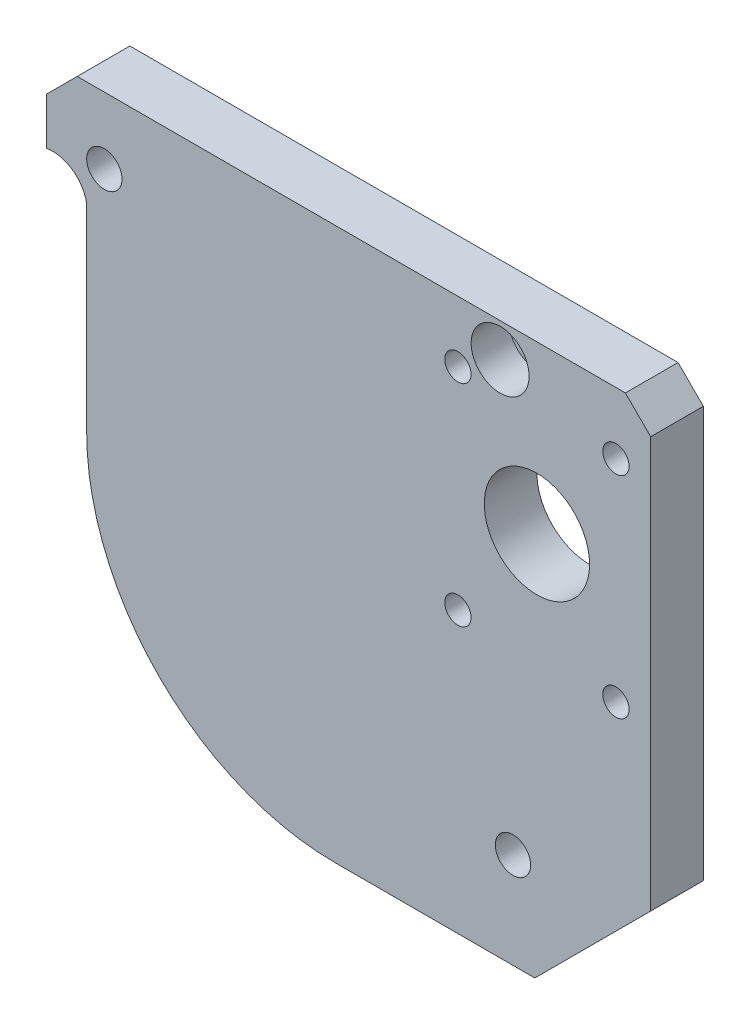
SolidWorks part; units mm, degrees
ref_plane "Front Plane" through (0, 0, 0) normal (0, 0, 1) x (1, 0, 0)
ref_plane "Top Plane" through (0, 0, 0) normal (0, 1, 0) x (1, 0, 0)
ref_plane "Right Plane" through (0, 0, 0) normal (1, 0, 0) x (0, 0, -1)
sketch "Sketch1" plane through (0, 0, 0) normal (0, 0, 1) x (1, 0, 0)
  line L0 (0, 0) -> (0, 66.548)
  line L1 (0, 66.548) -> (72.8218, 66.548)
  line L2 (72.8218, 66.548) -> (72.8218, 0)
  line L3 (72.8218, 0) -> (0, 0)
  dimension "D1" = 66.548
  dimension "D2" = 72.8218
extrude "Boss-Extrude1" add sketch "Sketch1" along normal blind 6.35
sketch "Sketch2" plane through (0, 0, 6.35) normal (0, 0, 1) x (1, 0, 0)
  line L0 (72.8218, 0) -> (72.8218, 66.548) construction
  line L1 (72.8218, 66.548) -> (0, 66.548) construction
  circle A0 centre (59.1058, 46.482) radius 6.35
  dimension "D1" = 12.7
  dimension "D2" = 13.716
  dimension "D3" = 20.066
extrude "Cut-Extrude1" cut sketch "Sketch2" against normal through all
sketch "Sketch3" plane through (0, 0, 6.35) normal (0, 0, 1) x (1, 0, 0)
  line L0 (0, 0) -> (72.8218, 0) construction
  line L1 (72.8218, 0) -> (72.8218, 66.548) construction
  circle A0 centre (56.2166, 11.5252) radius 2.1272
  dimension "D1" = 4.2545
  dimension "D2" = 11.5252
  dimension "D3" = 16.6052
extrude "Cut-Extrude2" cut sketch "Sketch3" against normal through all
sketch "Sketch4" plane through (0, 0, 6.35) normal (0, 0, 1) x (1, 0, 0)
  line L0 (0, 66.548) -> (0, 0) construction
  line L1 (72.8218, 66.548) -> (0, 66.548) construction
  circle A0 centre (6.9532, 58.5152) radius 2.1273
  dimension "D1" = 4.2545
  dimension "D2" = 6.9532
  dimension "D3" = 8.0328
extrude "Cut-Extrude3" cut sketch "Sketch4" against normal through all
sketch "Sketch5" plane through (0, 0, 6.35) normal (0, 0, 1) x (1, 0, 0)
  line L0 (72.8218, 66.548) -> (0, 66.548) construction
  line L1 (72.8218, 0) -> (72.8218, 66.548) construction
  circle A0 centre (54.6672, 62.465) radius 2.1272
  dimension "D1" = 4.2545
  dimension "D2" = 4.0831
  dimension "D3" = 18.1546
extrude "Cut-Extrude4" cut sketch "Sketch5" against normal through all
sketch "Sketch6" plane through (0, 0, 6.35) normal (0, 0, 1) x (1, 0, 0)
  circle A0 centre (54.6672, 62.465) radius 3.4925
  dimension "D1" = 6.985
extrude "Cut-Extrude5" cut sketch "Sketch6" against normal blind 4.572
hole_wizard "1/8 (0.125) Diameter Hole1" positions "Sketch8" profile "Sketch7" hole size "1/8" standard "Ansi Inch"
sketch "Sketch8" plane through (0, 0, 6.35) normal (0, 0, 1) x (1, 0, 0)
  circle A0 centre (59.1058, 46.482) radius 6.35 construction
  point P0 (49.5808, 59.182)
  point P1 (68.6308, 59.1091)
  point P3 (68.6307, 33.7091)
  point P5 (49.5808, 33.782)
  dimension "D1" = 12.7
  dimension "D2" = 9.525
  dimension "D3" = 19.05
  dimension "D4" = 25.4
  dimension "D5" = 19.05
  dimension "D6" = 25.4
  dimension "D7" = 9.525
sketch "Sketch7" plane through (49.5808, 59.182, 6.35) normal (1, 0, 0) x (0, -1, 0)
  line L0 (0, 0) -> (0, 26.3539)
  line L1 (0, 26.3539) -> (1.5875, 25.4)
  line L2 (1.5875, 25.4) -> (1.5875, 0)
  line L5 (1.5875, 0) -> (0, 0)
  line L10 (0, 26.3539) -> (-1.5875, 25.4) construction
  line L11 (0, -6.35) -> (0, 107.95) construction
  dimension "Hole Dia." = 3.175
  dimension "Hole Depth" = 25.4
  dimension "Drill Angle" = 118
sketch "Sketch9" plane through (0, 0, 6.35) normal (0, 0, 1) x (1, 0, 0)
  line L0 (72.8218, 13.97) -> (58.8518, 0)
  line L1 (72.8218, 0) -> (72.8218, 66.548) construction
  line L2 (0, 0) -> (72.8218, 0) construction
  line L3 (58.8518, 0) -> (72.8218, 0)
  line L4 (72.8218, 0) -> (72.8218, 13.97)
  dimension "D1" = 13.97
extrude "Cut-Extrude6" cut sketch "Sketch9" against normal through all
sketch "Sketch10" plane through (0, 0, 6.35) normal (0, 0, 1) x (1, 0, 0)
  line L0 (3.683, 66.548) -> (0, 62.865)
  line L1 (72.8218, 66.548) -> (0, 66.548) construction
  line L2 (0, 66.548) -> (0, 0) construction
  line L3 (0, 62.865) -> (0, 66.548)
  line L4 (0, 66.548) -> (3.683, 66.548)
  dimension "D1" = 3.683
extrude "Cut-Extrude7" cut sketch "Sketch10" against normal through all
sketch "Sketch11" plane through (0, 0, 6.35) normal (0, 0, 1) x (1, 0, 0)
  line L0 (4.826, 0) -> (4.826, 24.6833) construction
  line L2 (0, 62.865) -> (0, 0) construction
  line L3 (-5.4083, 57.1925) -> (14.8838, 57.1925) construction
  line L4 (4.826, 53.831) -> (4.826, 0)
  line L5 (0, 0) -> (58.8518, 0) construction
  line L6 (4.826, 0) -> (0, 0)
  line L7 (0, 0) -> (0, 57.1925)
  arc A0 (0, 57.1925) -> (4.826, 53.831) centre (0.7323, 53.0988) cw
  dimension "D1" = 4.826
extrude "Cut-Extrude8" cut sketch "Sketch11" against normal through all
sketch "Sketch12" plane through (0, 0, 6.35) normal (0, 0, 1) x (1, 0, 0)
  line L0 (34.798, -3.0915) -> (34.798, 28.3696) construction
  line L1 (4.826, 0) -> (4.826, 53.831) construction
  line L2 (-7.3402, 29.972) -> (13.905, 29.972) construction
  line L3 (4.826, 0) -> (58.8518, 0) construction
  line L4 (4.826, 29.972) -> (4.826, 0)
  line L5 (4.826, 0) -> (34.798, 0)
  arc A0 (34.798, 0) -> (4.826, 29.972) centre (34.798, 29.972) cw
  dimension "D1" = 29.972
  dimension "D2" = 29.972
extrude "Cut-Extrude9" cut sketch "Sketch12" against normal through all
sketch "Sketch13" plane through (0, 0, 6.35) normal (0, 0, 1) x (1, 0, 0)
  line L0 (69.7738, 66.548) -> (72.8218, 63.5)
  line L1 (72.8218, 66.548) -> (3.683, 66.548) construction
  line L2 (72.8218, 13.97) -> (72.8218, 66.548) construction
  line L3 (69.7738, 66.548) -> (72.8218, 66.548)
  line L4 (72.8218, 66.548) -> (72.8218, 63.5)
  dimension "D1" = 3.048
extrude "Cut-Extrude10" cut sketch "Sketch13" against normal through all
